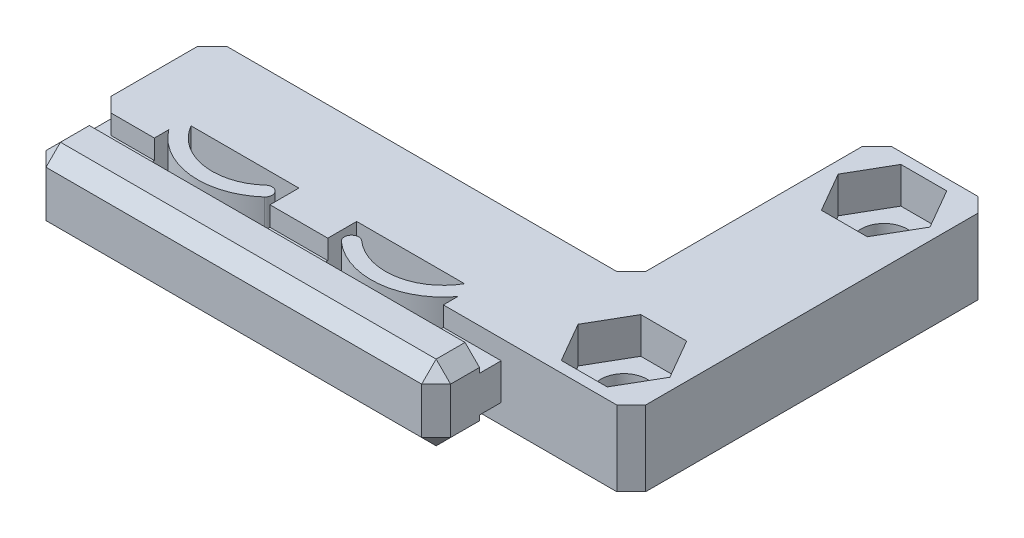
SolidWorks part; units mm, degrees
ref_plane "Front Plane" through (0, 0, 0) normal (0, 0, 1) x (1, 0, 0)
ref_plane "Top Plane" through (0, 0, 0) normal (0, 1, 0) x (1, 0, 0)
ref_plane "Right Plane" through (0, 0, 0) normal (1, 0, 0) x (0, 0, -1)
sketch "Sketch1" plane through (0, 0, 0) normal (0, 1, 0) x (1, 0, 0)
  line L0 (0, 0) -> (0, 25)
  line L1 (0, 25) -> (-8, 25)
  line L2 (-8, 25) -> (-8, 8)
  line L3 (-8, 8) -> (-37, 8)
  line L4 (-37, 8) -> (-37, 0)
  line L5 (-37, 0) -> (-33, 0)
  line L6 (-25, 0) -> (-21, 0)
  line L8 (-33, 0) -> (-33, 2)
  line L9 (-33, 2) -> (-25, 2)
  line L10 (-25, 0) -> (-25, 2)
  line L12 (-21, 0) -> (-21, 2)
  line L13 (-21, 2) -> (-13, 2)
  line L14 (-13, 0) -> (-13, 2)
  line L15 (-13, 0) -> (0, 0)
  dimension "D1" = 25
  dimension "D2" = 8
  dimension "D3" = 8
  dimension "D4" = 2
  dimension "D5" = 8
  dimension "D6" = 8
  dimension "D7" = 4
  dimension "D8" = 5
  dimension "D9" = 4
extrude "Boss-Extrude1" add sketch "Sketch1" along normal mid plane 5.2
sketch "Sketch2" plane through (-13, 0, 0) normal (-1, 0, 0) x (0, 0, 1)
  line L0 (1.5, -1.25) -> (1.5, -2.6)
  line L1 (0, 1.25) -> (1.5, 1.25)
  line L2 (0, 1.25) -> (0, -1.25)
  line L3 (0, -1.25) -> (1.5, -1.25)
  line L4 (0, 2.6) -> (0, -2.6) construction
  line L5 (1.5, 2.6) -> (4.5, 2.6)
  line L6 (1.5, 2.6) -> (1.5, 1.25)
  line L7 (1.5, -2.6) -> (4.5, -2.6)
  line L8 (4.5, 2.6) -> (4.5, -2.6)
  line L9 (-2, 2.6) -> (0, 2.6) construction
  line L10 (-2, -2.6) -> (0, -2.6) construction
  point P1 (0, 0)
  dimension "D1" = 3
  dimension "D2" = 1.5
  dimension "D3" = 2.5
extrude "Boss-Extrude2" add sketch "Sketch2" against normal blind 4
sketch "Sketch3" plane through (-25, 0, 0) normal (-1, 0, 0) x (0, 0, 1)
  line L0 (0, 1.25) -> (0, -1.25)
  line L1 (0, -1.25) -> (1.5, -1.25)
  line L2 (1.5, -1.25) -> (1.5, -2.6)
  line L3 (1.5, -2.6) -> (4.5, -2.6)
  line L4 (4.5, -2.6) -> (4.5, 2.6)
  line L5 (4.5, 2.6) -> (1.5, 2.6)
  line L6 (1.5, 2.6) -> (1.5, 1.25)
  line L7 (1.5, 1.25) -> (0, 1.25)
extrude "Boss-Extrude3" add sketch "Sketch3" against normal blind 4
ref_plane "Plane1" through (-23, 0, 0) normal (-1, 0, 0) x (0, 0, 1)
sketch "Sketch4" plane through (-13, 0, 0) normal (-1, 0, 0) x (0, 0, 1)
  line L1 (1.5, 2.6) -> (4.5, 2.6)
  line L2 (1.5, 2.6) -> (1.5, -2.6)
  line L3 (1.5, -2.6) -> (4.5, -2.6)
  line L4 (4.5, 2.6) -> (4.5, -2.6)
extrude "Boss-Extrude4" add sketch "Sketch4" along normal blind 8
sketch "Sketch5" plane through (0, 0, 0) normal (0, 1, 0) x (1, 0, 0)
  line L0 (-13, 1) -> (-13, 2)
  line L1 (-13, 2) -> (-13.5359, 2)
  line L2 (-21, 2) -> (-13, 2) construction
  line L3 (-21, 0) -> (-21, 2) construction
  arc A0 (-13, 1) -> (-20.3333, 0.2732) centre (-17, 4) cw
  arc A1 (-20.3333, 0.2732) -> (-19.6667, 1.0186) centre (-20, 0.6459) cw
  arc A2 (-19.6667, 1.0186) -> (-13.5359, 2) centre (-17, 4) ccw
  point P13 (-17, 2)
  dimension "D1" = 1
  dimension "D2" = 2
  dimension "D3" = 5
  dimension "D4" = 0.5
extrude "Boss-Extrude5" add sketch "Sketch5" along normal mid plane 5.2
mirror "Mirror1" about plane through (-23, 0, 0) normal (-1, 0, 0) of "Boss-Extrude5", "Boss-Extrude2", "Boss-Extrude4"
sketch "Sketch6" plane through (0, 2.6, 0) normal (0, 1, 0) x (1, 0, 0)
  line L0 (-4, 25) -> (-4, 0) construction
  line L1 (0, 25) -> (-8, 25) construction
  line L2 (-13, 0) -> (0, 0) construction
  line L3 (-4, 21.5) -> (-4, 3.5) construction
  circle A0 centre (-4, 21.5) radius 1.6
  circle A1 centre (-4, 3.5) radius 1.6
  point P10 (-4, 12.5)
  dimension "D1" = 3.2
  dimension "D2" = 18
extrude "Cut-Extrude1" cut sketch "Sketch6" against normal through all
sketch "Sketch7" plane through (0, 2.6, 0) normal (0, 1, 0) x (1, 0, 0)
  line L1 (-0.8246, 3.5) -> (-2.4123, 6.25)
  line L2 (-2.4123, 6.25) -> (-5.5877, 6.25)
  line L3 (-5.5877, 6.25) -> (-7.1754, 3.5)
  line L4 (-7.1754, 3.5) -> (-5.5877, 0.75)
  line L5 (-5.5877, 0.75) -> (-2.4123, 0.75)
  line L6 (-2.4123, 0.75) -> (-0.8246, 3.5)
  line L7 (-0.8246, 21.5) -> (-2.4123, 24.25)
  line L8 (-2.4123, 24.25) -> (-5.5877, 24.25)
  line L9 (-5.5877, 24.25) -> (-7.1754, 21.5)
  line L10 (-7.1754, 21.5) -> (-5.5877, 18.75)
  line L11 (-5.5877, 18.75) -> (-2.4123, 18.75)
  line L12 (-2.4123, 18.75) -> (-0.8246, 21.5)
  circle A0 centre (-4, 3.5) radius 2.75 construction
  circle A1 centre (-4, 21.5) radius 2.75 construction
  dimension "D1" = 5.5
extrude "Cut-Extrude2" cut sketch "Sketch7" against normal blind 2.5
chamfer "Chamfer1" distance 1 angle 45 15 edges at (-9, 0, 4.5) (-9, -2.6, 3) (-23, -2.6, 4.5) (-9, 2.6, 3) (-23, 2.6, 4.5) (-37, -2.6, 3) (-37, 2.6, 3) (-37, 0, 4.5) (-37, 1.925, 0) (-37, -1.925, 0) (-37, 0, -8) (-8, 0, -8) (0, 0, 0) (0, 0, -25) (-8, 0, -25)
